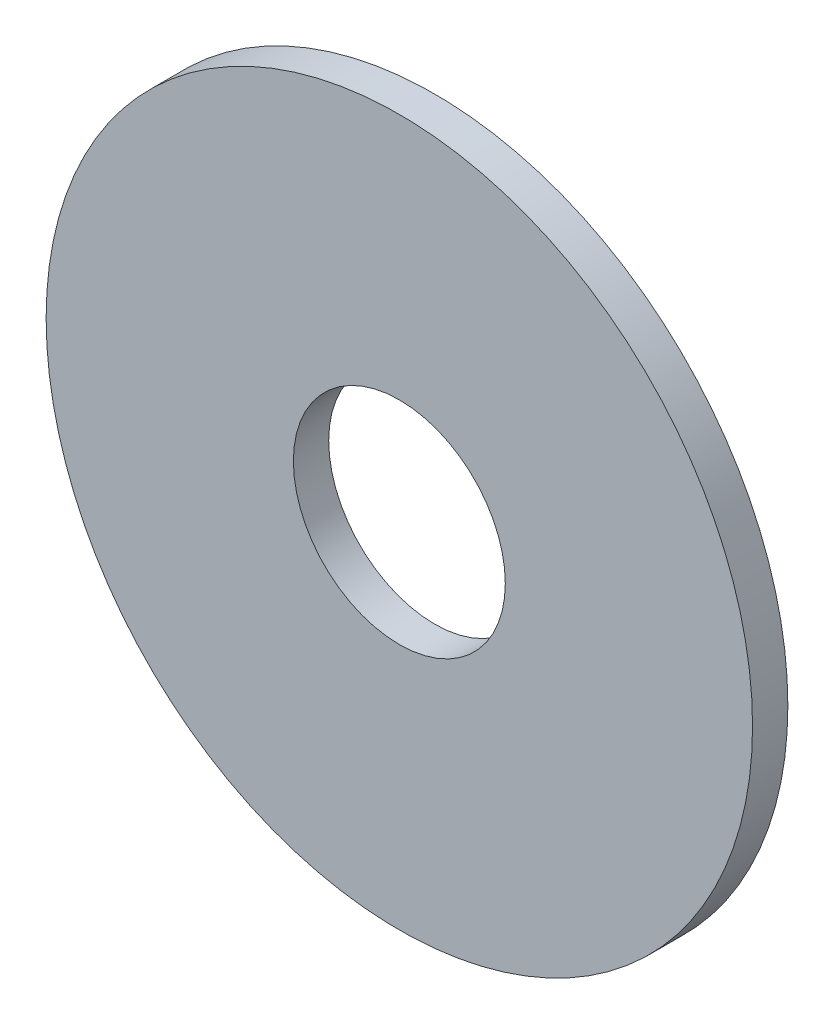
SolidWorks part; units mm, degrees
ref_plane "Front Plane" through (0, 0, 0) normal (0, 0, 1) x (1, 0, 0)
ref_plane "Top Plane" through (0, 0, 0) normal (0, 1, 0) x (1, 0, 0)
ref_plane "Right Plane" through (0, 0, 0) normal (1, 0, 0) x (0, 0, -1)
sketch "Sketch4" plane through (0, 0, 0) normal (0, 0, 1) x (1, 0, 0)
  circle A0 centre (0, 0) radius 100
  dimension "D1" = 200
extrude "Boss-Extrude1" add sketch "Sketch4" along normal blind 10
sketch "Sketch5" plane through (0, 0, 10) normal (0, 0, 1) x (1, 0, 0)
  circle A0 centre (0, 0) radius 30
extrude "Cut-Extrude1" cut sketch "Sketch5" against normal blind 10
